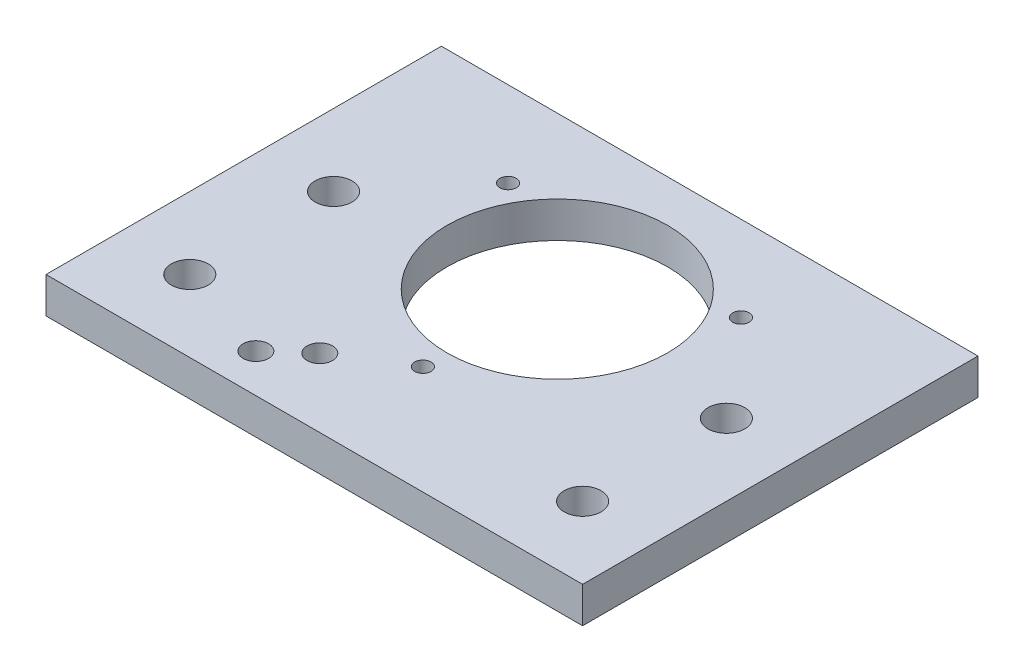
SolidWorks part; units mm, degrees
ref_plane "Front Plane" through (0, 0, 0) normal (0, 0, 1) x (1, 0, 0)
ref_plane "Top Plane" through (0, 0, 0) normal (0, 1, 0) x (1, 0, 0)
ref_plane "Right Plane" through (0, 0, 0) normal (1, 0, 0) x (0, 0, -1)
sketch "Sketch1" plane through (0, 0, 0) normal (0, 1, 0) x (1, 0, 0)
  line L0 (-34.7, 3.175) -> (34.7, 3.175) construction
  line L1 (-47.4, 34.925) -> (47.4, 34.925)
  line L2 (-47.4, 34.925) -> (-47.4, -34.925)
  line L3 (-47.4, -34.925) -> (47.4, -34.925)
  line L4 (47.4, 34.925) -> (47.4, -34.925)
  line L5 (-47.4, 34.925) -> (47.4, -34.925) construction
  line L6 (-47.4, -34.925) -> (47.4, 34.925) construction
  line L7 (22, -34.925) -> (47.4, -34.925) construction
  line L8 (-17.1383, -28.1118) -> (-11.1649, -22.7903) construction
  line L9 (-34.7, -22.225) -> (34.7, -22.225) construction
  line L10 (-34.7, -22.225) -> (-34.7, 22.225) construction
  line L11 (-34.7, 22.225) -> (34.7, 22.225) construction
  line L12 (34.7, -22.225) -> (34.7, 22.225) construction
  line L13 (-34.7, -22.225) -> (34.7, 22.225) construction
  line L14 (-34.7, 22.225) -> (34.7, -22.225) construction
  line L15 (0, 0) -> (0, 8) construction
  line L16 (-19.7991, -25.1251) -> (-13.8257, -19.8036) construction
  line L17 (22, -34.925) -> (22, -9.525) construction
  line L18 (22, -9.525) -> (47.4, -9.525) construction
  line L19 (47.4, -34.925) -> (47.4, -9.525) construction
  line L20 (22, -34.925) -> (47.4, -9.525) construction
  line L21 (22, -9.525) -> (47.4, -34.925) construction
  line L22 (0, 8) -> (0, -15.75) construction
  line L23 (0, 8) -> (20.5681, 19.875) construction
  line L24 (0, 8) -> (-20.5681, 19.875) construction
  line L25 (-14.4776, -31.0985) -> (-8.5042, -25.7771) construction
  line L27 (-47.4, -34.925) -> (-22, -34.925)
  line L28 (-47.4, -34.925) -> (-47.4, -9.525)
  line L29 (-47.4, -9.525) -> (-22, -9.525) construction
  line L30 (-22, -34.925) -> (-22, -9.525) construction
  circle A18 centre (-34.7, 22.225) radius 3.2576 construction
  circle A19 centre (34.7, 22.225) radius 3.2576 construction
  circle A20 centre (34.7, -22.225) radius 3.2576
  circle A21 centre (-34.7, -22.225) radius 3.2576
  circle A22 centre (-11.1649, -22.7903) radius 2.25
  circle A24 centre (0, 8) radius 19.5
  circle A25 centre (0, 8) radius 23.75 construction
  circle A30 centre (-34.7, 3.175) radius 3.2576
  circle A31 centre (34.7, 3.175) radius 3.2576
  circle A32 centre (0, -15.75) radius 1.45
  circle A33 centre (-20.5681, 19.875) radius 1.45
  circle A34 centre (20.5681, 19.875) radius 1.45
  circle A35 centre (0, 8) radius 26.5 construction
  circle A36 centre (-17.1383, -28.1118) radius 2.25
  arc A37 (-19.7991, -25.1251) -> (-14.4776, -31.0985) centre (-17.1383, -28.1118) ccw construction
  arc A38 (-8.5042, -25.7771) -> (-13.8257, -19.8036) centre (-11.1649, -22.7903) ccw construction
  circle A39 centre (-11.1649, -22.7903) radius 6 construction
  point P11 (-14.1516, -25.4511)
  point P51 (0, 34.5)
  dimension "D2" = 8
  dimension "D4" = 39
  dimension "D7" = 47.5
  dimension "D10" = 120
  dimension "D13" = 12.7
  dimension "D15" = 6.5151
  dimension "D16" = 4
  dimension "D17" = 4.5
  dimension "D9" = 120
  dimension "D5" = 8
  dimension "D12" = 2.9
  dimension "D18" = 53
  dimension "D19" = 12
  dimension "D6" = 94.8
  dimension "D8" = 69.85
  dimension "D11" = 25.4
  dimension "D14" = 12.7
  dimension "D3" = 25.4
extrude "Boss-Extrude1" add sketch "Sketch1" along normal blind 6.35 contours L4 L1 L2 L3 A36 A34 A33 A32 A31 A30 A24 A22 A21 A20
sketch "Sketch4" plane through (0, 0, 0) normal (0, -1, 0) x (1, 0, 0)
  line L6 (-17.1383, 28.1118) -> (-11.1649, 22.7903) construction
  line L7 (-14.145, 31.4719) -> (-8.1716, 26.1504)
  line L8 (-20.1317, 24.7518) -> (-14.1582, 19.4303)
  circle A6 centre (-11.1649, 22.7903) radius 2.25 construction
  circle A7 centre (-17.1383, 28.1118) radius 2.25 construction
  circle A8 centre (-11.1649, 22.7903) radius 2.25
  circle A9 centre (-17.1383, 28.1118) radius 2.25
  arc A10 (-14.145, 31.4719) -> (-20.1317, 24.7518) centre (-17.1383, 28.1118) ccw
  arc A11 (-14.1582, 19.4303) -> (-8.1716, 26.1504) centre (-11.1649, 22.7903) ccw
  point P23 (-14.1516, 25.4511)
  dimension "D2" = 4.5
extrude "Cut-Extrude2" cut sketch "Sketch4" against normal blind 3
equation "\"testbed_height\" = 91.50mm"
equation "\"plate_thickness\" = 6mm"
equation "\"main_body_splay_length\" = 48.5mm"
equation "\"splay_shaft_length_no_wires\" = 10mm"
equation "\"splay_shaft_length_wires\" = 6.5mm"
equation "\"timing_pulley_offset\" = 0mm"
equation "\"effective_motor_length\" = \"timing_pulley_offset\" + \"splay_shaft_length_no_wires\" + \"main_body_splay_length\""
equation "\"80_20_side\" = 25.4mm"
equation "\"80_20_length\" = 152.4mm"
equation "\"80_20_optic_mount_length\" = \"80_20_length\" - 25.4mm"
equation "\"optic_board_hole_size\" = 6.35mm"
equation "\"total_mounting_length\" = \"testbed_height\" - \"effective_motor_length\" - \"80_20_side\""
equation "\"mounting_vertical_portion_height\" = \"total_mounting_length\" - 2 * \"plate_thickness\""
equation "\"face_mount_width\" = 15.25mm"
equation "\"center_dist_to_face_mount_vertical_screws\" = 5mm"
equation "\"D1@Boss-Extrude1\"=0.25in"
